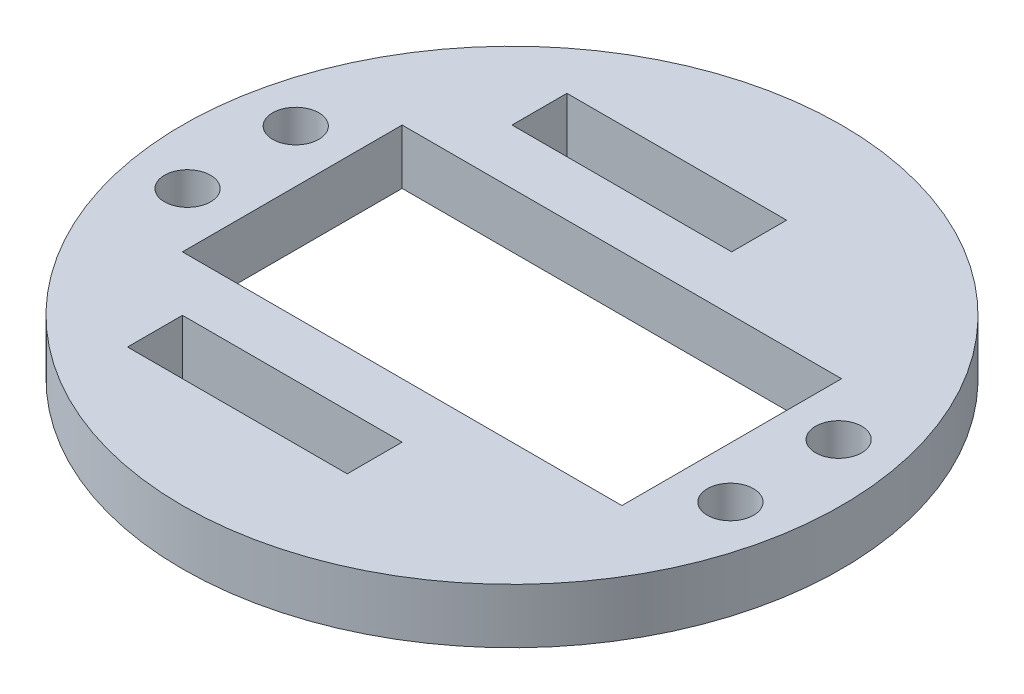
SolidWorks part; units mm, degrees
ref_plane "Front Plane" through (0, 0, 0) normal (0, 0, 1) x (1, 0, 0)
ref_plane "Top Plane" through (0, 0, 0) normal (0, 1, 0) x (1, 0, 0)
ref_plane "Right Plane" through (0, 0, 0) normal (1, 0, 0) x (0, 0, -1)
sketch "Sketch2" plane through (0, 0, 0) normal (0, 1, 0) x (1, 0, 0)
  circle A0 centre (0, 0) radius 30
  dimension "D1" = 60
extrude "Boss-Extrude1" add sketch "Sketch2" along normal blind 5 contours A0
sketch "Sketch3" plane through (0, 5, 0) normal (0, 1, 0) x (1, 0, 0)
  line L0 (0, 30) -> (0, -30) construction
  line L1 (-30, 0) -> (30, 0) construction
  line L3 (-20, -10) -> (20, -10)
  line L4 (-20, -10) -> (-20, 10)
  line L5 (-20, 10) -> (20, 10)
  line L6 (20, -10) -> (20, 10)
  line L7 (-20, -10) -> (20, 10) construction
  line L8 (-20, 10) -> (20, -10) construction
  circle A0 centre (0, 0) radius 30 construction
  point P7 (0, 0)
  dimension "D1" = 40
  dimension "D2" = 20
extrude "Cut-Extrude1" cut sketch "Sketch3" against normal through all
sketch "Sketch4" plane through (0, 5, 0) normal (0, 1, 0) x (1, 0, 0)
  line L0 (0, 30) -> (0, -30) construction
  line L1 (-30, 0) -> (30, 0) construction
  line L2 (-15, 20) -> (5, 20)
  line L3 (5, 20) -> (5, 15)
  line L4 (5, 15) -> (-15, 15)
  line L5 (-15, 15) -> (-15, 20)
  line L6 (5, -15) -> (-15, -15)
  line L7 (5, -20) -> (5, -15)
  line L8 (-15, -20) -> (5, -20)
  line L9 (-15, -15) -> (-15, -20)
  circle A0 centre (0, 0) radius 30 construction
  dimension "D1" = 20
  dimension "D2" = 5
  dimension "D3" = 20
  dimension "D4" = 15
extrude "Cut-Extrude2" cut sketch "Sketch4" against normal blind 10
sketch "Sketch5" plane through (0, 0, 0) normal (0, -1, 0) x (1, 0, 0)
  circle A0 centre (-24.7611, -5.075) radius 2.1
  circle A1 centre (-24.7611, 4.775) radius 2.1
  circle A2 centre (24.6611, 4.775) radius 2.1
  circle A3 centre (24.6611, -5.075) radius 2.1
  dimension "D1" = 4.2
  dimension "D2" = 4.2
  dimension "D3" = 4.2
extrude "Cut-Extrude3" cut sketch "Sketch5" against normal through all
